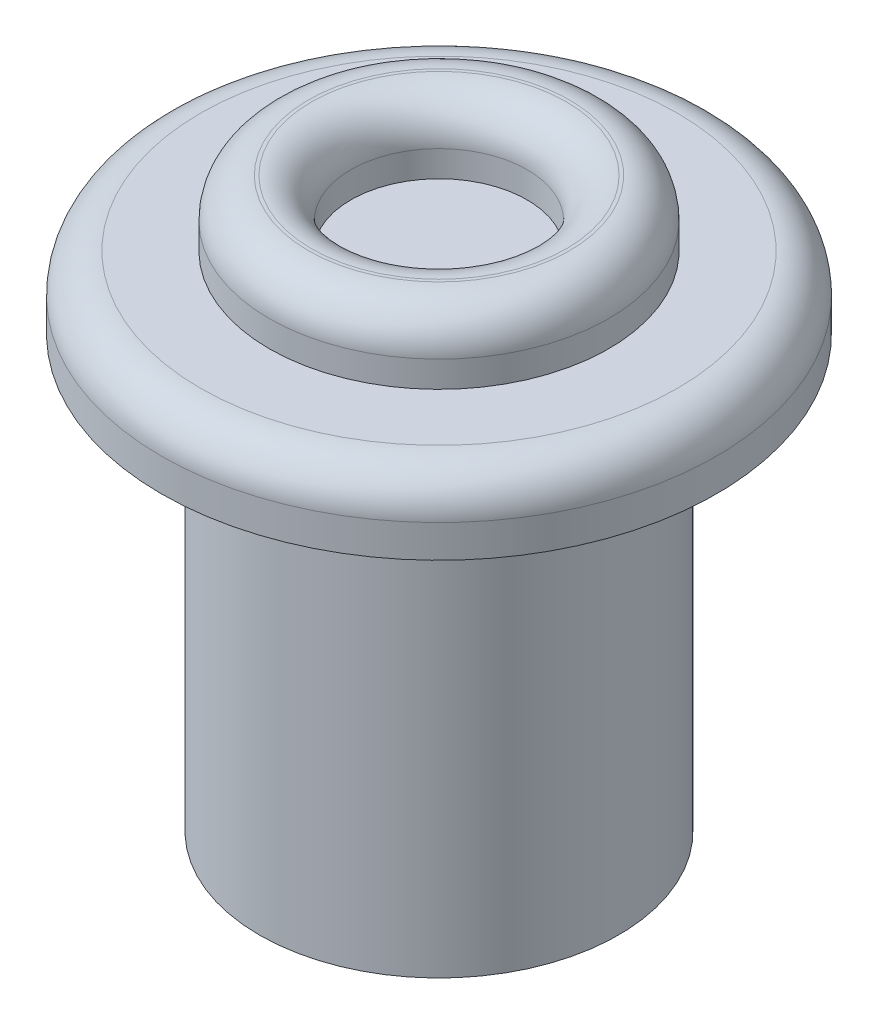
SolidWorks part; units mm, degrees
ref_plane "Front Plane" through (0, 0, 0) normal (0, 0, 1) x (1, 0, 0)
ref_plane "Top Plane" through (0, 0, 0) normal (0, 1, 0) x (1, 0, 0)
ref_plane "Right Plane" through (0, 0, 0) normal (1, 0, 0) x (0, 0, -1)
sketch "Sketch1" plane through (0, 0, 0) normal (0, 1, 0) x (1, 0, 0)
  circle A0 centre (0, 0) radius 2.75
  circle A1 centre (0, 0) radius 1.4
  point P4 (0, 0)
  dimension "D1" = 5.5
  dimension "D2" = 1.35
extrude "Boss-Extrude1" add sketch "Sketch1" along normal blind 6.6
sketch "Sketch2" plane through (0, 6.6, 0) normal (0, 1, 0) x (1, 0, 0)
  circle A0 centre (0, 0) radius 4.25
  dimension "D1" = 8.5
extrude "Boss-Extrude2" add sketch "Sketch2" along normal blind 1.1
sketch "Sketch3" plane through (0, 7.7, 0) normal (0, 1, 0) x (1, 0, 0)
  circle A0 centre (0, 0) radius 2.6
  circle A1 centre (0, 0) radius 1.35
  dimension "D1" = 5.2
  dimension "D2" = 1.25
extrude "Boss-Extrude3" add sketch "Sketch3" along normal blind 1
fillet "Fillet1" radius 0.6 3 edges at (0, 8.7, 1.35) (0, 8.7, 2.6) (0, 7.7, 4.25)
